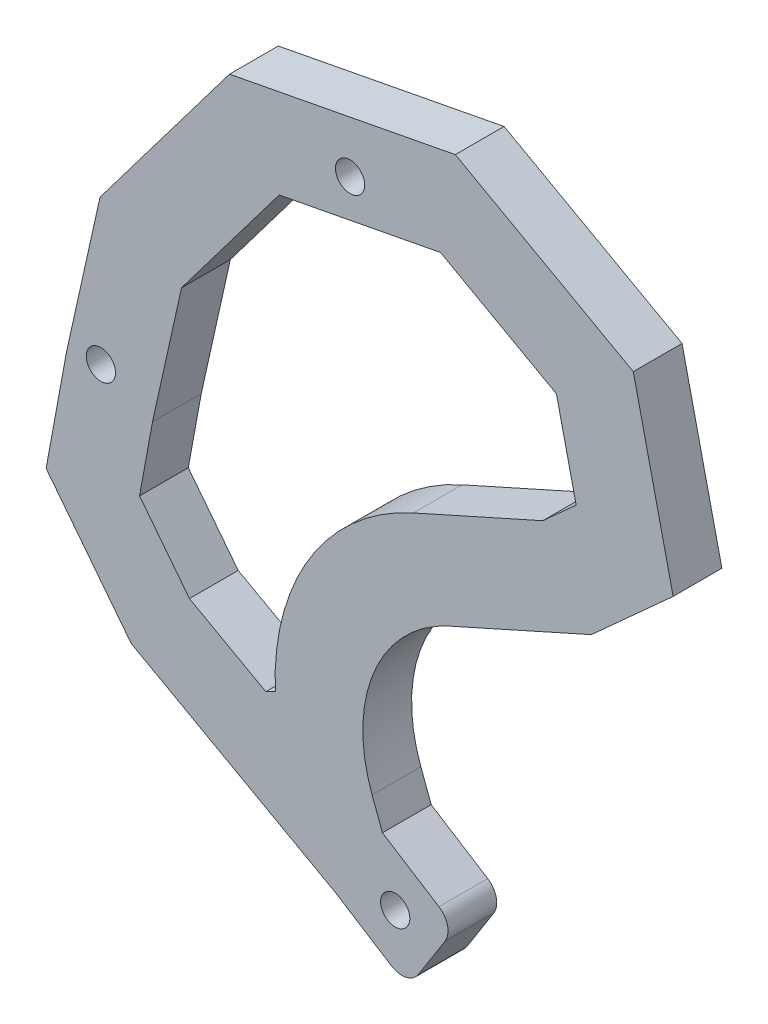
SolidWorks part; units mm, degrees
material "PMMA"
ref_plane "Front Plane" through (0, 0, 0) normal (0, 0, 1) x (1, 0, 0)
ref_plane "Top Plane" through (0, 0, 0) normal (0, 1, 0) x (1, 0, 0)
ref_plane "Right Plane" through (0, 0, 0) normal (1, 0, 0) x (0, 0, -1)
sketch "Sketch2" plane through (6.3019, 33.3416, -27) normal (0, 0, -1) x (-0.6708, 0.7416, 0)
  line L1 (-60.0143, -23.84) -> (-68.5495, -21.4689)
  line L2 (-62.4505, -32.6098) -> (-70.9857, -30.2387)
  line L3 (-68.5495, -21.4689) -> (-70.9857, -30.2387)
  line L4 (-60.0143, -23.84) -> (-70.9857, -30.2387) construction
  line L5 (-62.4505, -32.6098) -> (-68.5495, -21.4689) construction
  line L6 (-62.4505, -32.6098) -> (-39.8158, -40.3158)
  line L7 (-39.8158, -40.3158) -> (-25.6615, -39.2802)
  line L8 (-25.6615, -39.2802) -> (-18.6216, -30.0948)
  line L9 (-18.6216, -30.0948) -> (-9.4567, -17.167)
  line L10 (-9.4567, -17.167) -> (-5.3357, 4.4683)
  line L11 (-5.3357, 4.4683) -> (-17.5843, 24.6155)
  line L12 (-17.5843, 24.6155) -> (-22.7923, 26.3886)
  line L13 (-22.7923, 26.3886) -> (-37.3551, 31.3465)
  line L14 (-37.3551, 31.3465) -> (-53.39, 22.3515)
  line L15 (-53.39, 22.3515) -> (-53.39, 11.0408)
  line L16 (-60.0143, -23.84) -> (-57.1978, -22.724)
  line L17 (-48.4573, -4.1448) -> (-53.39, 11.0408)
  line L18 (-47.1303, -28.3183) -> (-38.6475, -31.2062)
  line L19 (-38.6475, -31.2062) -> (-30.3473, -30.599)
  line L20 (-30.3473, -30.599) -> (-25.8668, -24.753)
  line L21 (-25.8668, -24.753) -> (-17.9314, -13.5594)
  line L22 (-17.9314, -13.5594) -> (-14.8246, 2.7513)
  line L23 (-14.8246, 2.7513) -> (-23.5774, 17.1486)
  line L24 (-23.5774, 17.1486) -> (-25.6929, 17.8688)
  line L25 (-25.6929, 17.8688) -> (-36.4543, 21.5325)
  line L26 (-36.4543, 21.5325) -> (-44.39, 17.0808)
  line L27 (-44.39, 17.0808) -> (-44.39, 12.4659)
  line L28 (-39.8975, -1.3644) -> (-44.39, 12.4659)
  line L33 (-47.1303, -28.3183) -> (-47.398, -27.2486)
  line L34 (-48.2624, -27.9328) -> (-38.6475, -31.2062) construction
  line L35 (-48.2624, -27.9328) -> (-48.2624, -27.9328) construction
  line L36 (-48.2624, -27.9328) -> (-48.2624, -27.9328) construction
  line L37 (-48.2624, -27.9328) -> (-48.2624, -27.9328) construction
  line L38 (-48.2624, -27.9328) -> (-48.2624, -27.9328) construction
  circle A0 centre (-65.5, -27.0393) radius 1.5
  circle A1 centre (-20.5, -27.0393) radius 1.5
  circle A2 centre (-15.8, 11.6764) radius 1.5
  arc A3 (-48.4573, -4.1448) -> (-57.1978, -22.724) centre (-62.7235, -8.7789) cw
  arc A4 (-39.8975, -1.3644) -> (-47.398, -27.2486) centre (-62.7235, -8.7789) cw
  arc A5 (-39.8975, -1.3644) -> (-48.2624, -27.9328) centre (-62.7235, -8.7789) cw construction
  dimension "D1" = 3
  dimension "D2" = 3
  dimension "D3" = 3
  dimension "D4" = 15
  dimension "D5" = 9
extrude "Boss-Extrude1" add sketch "Sketch2" against normal blind 5
fillet "Fillet1" radius 2 2 edges at (36.3629, -31.8986, -24.5) (31.4932, -39.5882, -24.5)
